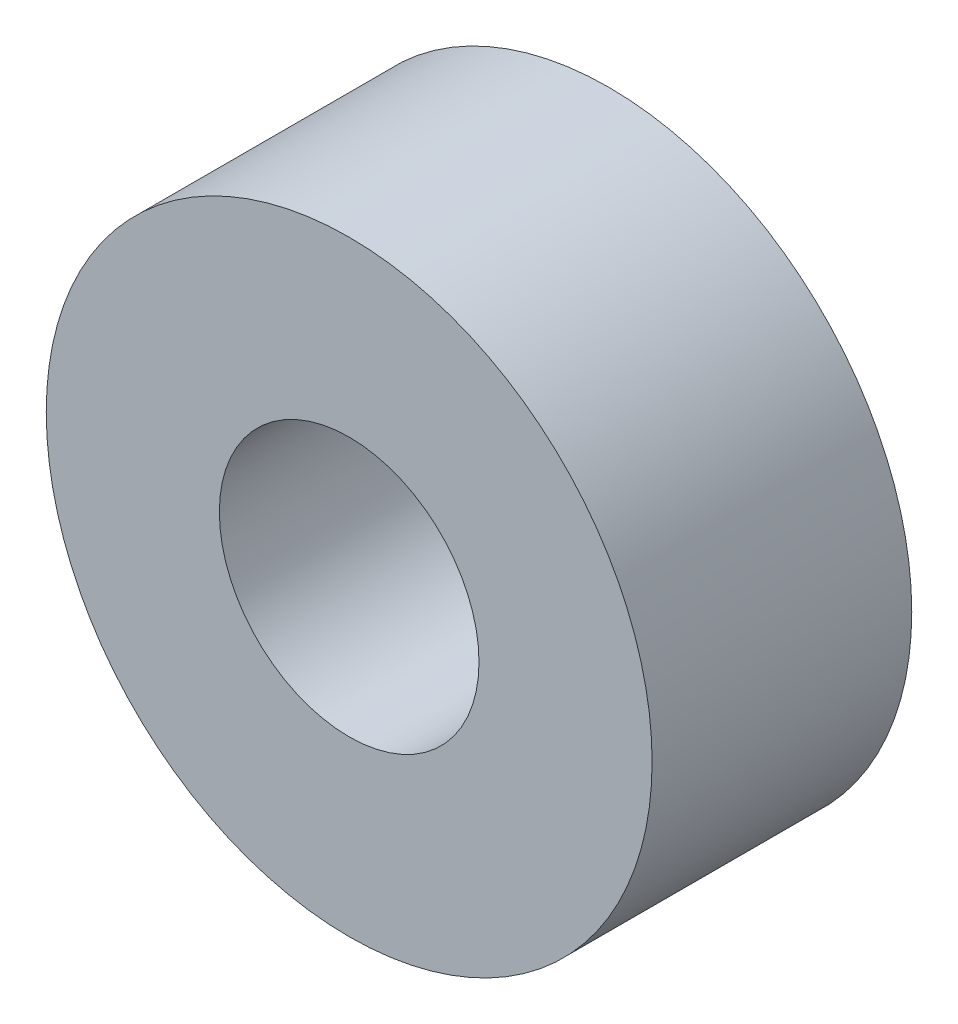
SolidWorks part; units mm, degrees
material "尼龙 101"
ref_plane "前视" through (0, 0, 0) normal (0, 0, 1) x (1, 0, 0)
ref_plane "上视" through (0, 0, 0) normal (0, 1, 0) x (1, 0, 0)
ref_plane "右视" through (0, 0, 0) normal (1, 0, 0) x (0, 0, -1)
sketch "草图1" plane through (0, 0, 0) normal (0, 0, 1) x (1, 0, 0)
  circle A0 centre (0, 0) radius 3.5
  circle A1 centre (0, 0) radius 1.5
  dimension "D1" = 3
  dimension "D2" = 7
extrude "凸台-拉伸1" add sketch "草图1" along normal blind 3
